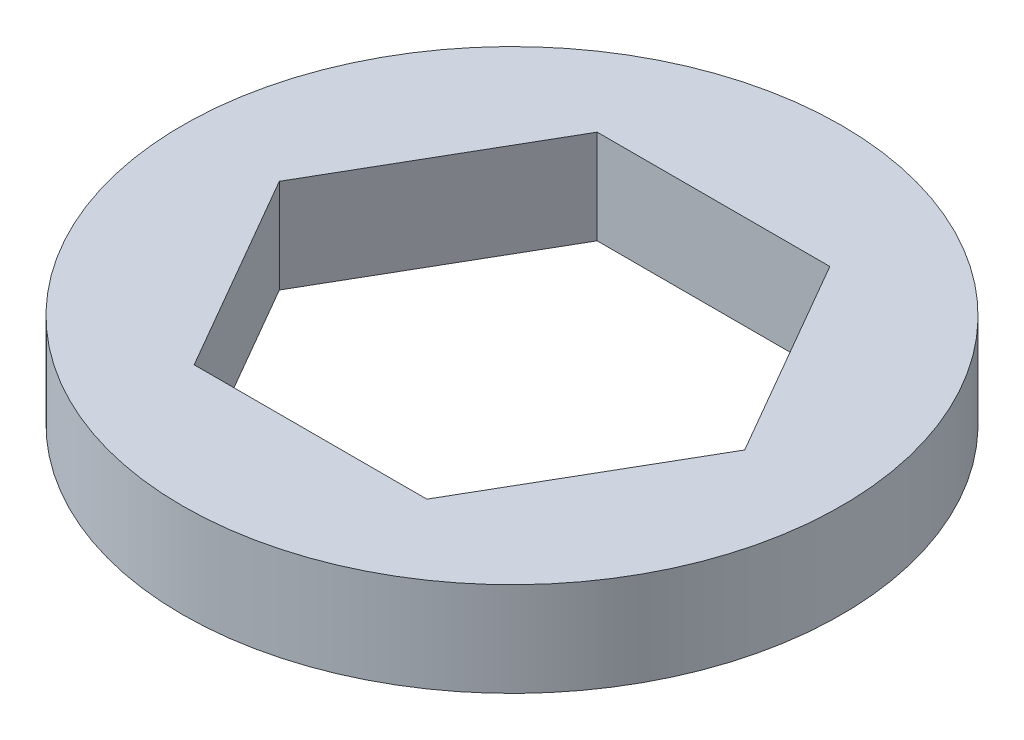
SolidWorks part; units mm, degrees
ref_plane "Front" through (0, 0, 0) normal (0, 0, 1) x (1, 0, 0)
ref_plane "Top" through (0, 0, 0) normal (0, 1, 0) x (1, 0, 0)
ref_plane "Right" through (0, 0, 0) normal (1, 0, 0) x (0, 0, -1)
sketch "Sketch1" plane through (0, 0, 0) normal (0, 1, 0) x (1, 0, 0)
  line L1 (7.8456, 0) -> (3.9228, 6.7945)
  line L2 (3.9228, 6.7945) -> (-3.9228, 6.7945)
  line L3 (-3.9228, 6.7945) -> (-7.8456, 0)
  line L4 (-7.8456, 0) -> (-3.9228, -6.7945)
  line L5 (-3.9228, -6.7945) -> (3.9228, -6.7945)
  line L6 (3.9228, -6.7945) -> (7.8456, 0)
  circle A0 centre (0, 0) radius 6.7945 construction
  circle A1 centre (0, 0) radius 11.1125
  dimension "D1" = 22.225
extrude "Boss-Extrude1" add sketch "Sketch1" along normal blind 3.175
